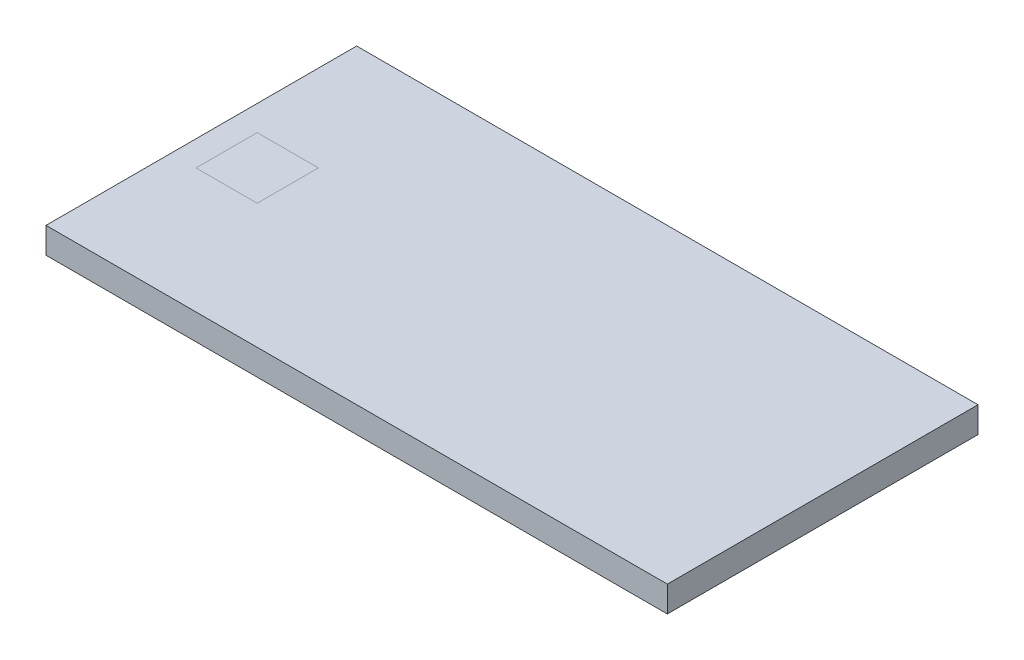
SolidWorks part; units mm, degrees
material "1023 Carbon Steel Sheet (SS)"
ref_plane "Front Plane" through (0, 0, 0) normal (0, 0, 1) x (1, 0, 0)
ref_plane "Top Plane" through (0, 0, 0) normal (0, 1, 0) x (1, 0, 0)
ref_plane "Right Plane" through (0, 0, 0) normal (1, 0, 0) x (0, 0, -1)
sketch "Sketch1" plane through (0, 0, 0) normal (1, 0, 0) x (0, 0, -1)
  line L0 (0, -1534.4769) -> (0, 75189.3682) construction
  line L1 (-457.2, 0) -> (457.2, 0)
  line L2 (457.2, 0) -> (457.2, -76.2)
  line L3 (457.2, -76.2) -> (381, -76.2)
  line L4 (-457.2, -76.2) -> (-381, -76.2)
  line L5 (-457.2, 0) -> (-457.2, -76.2)
  line L6 (-450.85, -69.85) -> (-381, -69.85)
  line L7 (-450.85, -6.35) -> (-450.85, -69.85)
  line L8 (-450.85, -6.35) -> (450.85, -6.35)
  line L9 (450.85, -6.35) -> (450.85, -69.85)
  line L10 (450.85, -69.85) -> (381, -69.85)
  line L11 (-381, -69.85) -> (-381, -76.2)
  line L12 (381, -69.85) -> (381, -76.2)
  point P10 (0, 0)
  dimension "D1" = 76.2
  dimension "D2" = 76.2
  dimension "D3" = 914.4
  dimension "D4" = 6.35
extrude "Boss-Extrude1" add sketch "Sketch1" along normal mid plane 1828.8
sketch "Sketch2" plane through (0, 0, 0) normal (0, 0, 1) x (1, 0, 0)
  line L0 (0, -1000) -> (0, 49000) construction
  line L1 (-914.4, 0) -> (-914.4, -76.2)
  line L2 (-914.4, -76.2) -> (-838.2, -76.2)
  line L3 (914.4, -76.2) -> (-914.4, -76.2) construction
  line L4 (-838.2, -76.2) -> (-838.2, -69.85)
  line L5 (-838.2, -69.85) -> (-908.05, -69.85)
  line L6 (-908.05, -69.85) -> (-908.05, 0)
  line L7 (914.4, 0) -> (-914.4, 0) construction
  line L8 (-908.05, 0) -> (-914.4, 0)
  line L9 (908.05, 0) -> (914.4, 0)
  line L10 (908.05, -69.85) -> (908.05, 0)
  line L11 (838.2, -69.85) -> (908.05, -69.85)
  line L12 (838.2, -76.2) -> (838.2, -69.85)
  line L13 (914.4, -76.2) -> (838.2, -76.2)
  line L14 (914.4, 0) -> (914.4, -76.2)
  dimension "D1" = 6.35
extrude "Boss-Extrude2" add sketch "Sketch2" along normal mid plane 914.4
sketch "Sketch3" plane through (0, 0, 0) normal (0, 1, 0) x (1, 0, 0)
  line L1 (-840, 90) -> (-660, 90)
  line L2 (-840, 90) -> (-840, -90)
  line L3 (-840, -90) -> (-660, -90)
  line L4 (-660, 90) -> (-660, -90)
  line L5 (-750, -90) -> (-750, 90) construction
  line L6 (-840, 0) -> (-660, 0) construction
  point P0 (-750, 0)
  dimension "D1" = 180
  dimension "D2" = 750
split line "Split Line1"
